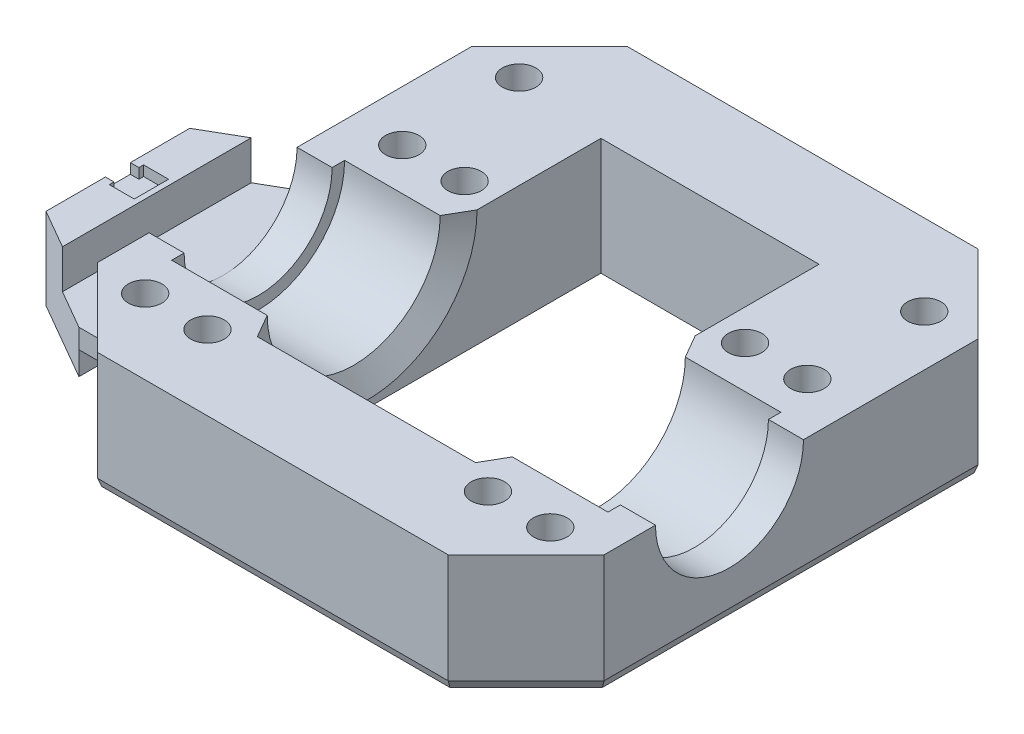
SolidWorks part; units mm, degrees
ref_plane "Спереди" through (0, 0, 0) normal (0, 0, 1) x (1, 0, 0)
ref_plane "Сверху" through (0, 0, 0) normal (0, 1, 0) x (1, 0, 0)
ref_plane "Справа" through (0, 0, 0) normal (1, 0, 0) x (0, 0, -1)
sketch "Sketch1" plane through (0, 0, 0) normal (0, 1, 0) x (1, 0, 0)
  line L1 (32.5, -50) -> (-32.5, -50)
  line L2 (32.5, -50) -> (32.5, 50)
  line L3 (32.5, 50) -> (-32.5, 50)
  line L4 (-32.5, -50) -> (-32.5, 50)
  line L5 (32.5, -50) -> (-32.5, 50) construction
  line L6 (32.5, 50) -> (-32.5, -50) construction
  line L7 (14, -40) -> (-14, -40)
  line L8 (14, -40) -> (14, 40)
  line L9 (14, 40) -> (-14, 40)
  line L10 (-14, -40) -> (-14, 40)
  line L11 (14, -40) -> (-14, 40) construction
  line L12 (14, 40) -> (-14, -40) construction
  point P0 (0, 0)
  point P6 (0, 0)
  dimension "D1" = 65
  dimension "D2" = 100
  dimension "D3" = 80
  dimension "D4" = 28
extrude "Boss-Extrude1" add sketch "Sketch1" along normal blind 15
sketch "Sketch3" plane through (0, 15, 0) normal (0, 1, 0) x (1, 0, 0)
  line L0 (-14, 0) -> (-32.5, 0) construction
  line L1 (-14, 40) -> (-14, -40) construction
  line L2 (-32.5, 50) -> (-32.5, -50) construction
  line L3 (14, 0) -> (32.5, 0) construction
  line L4 (14, -40) -> (14, 40) construction
  line L5 (32.5, -50) -> (32.5, 50) construction
  line L10 (14, -11.1) -> (28, -11.1)
  line L11 (14, -11.1) -> (14, 0)
  line L12 (14, 0) -> (28, 0)
  line L13 (28, -11.1) -> (28, 0)
  line L14 (14, -11.1) -> (28, 0) construction
  line L15 (14, 0) -> (28, -11.1) construction
  line L16 (-28, -11.1) -> (-14, -11.1)
  line L17 (-28, -11.1) -> (-28, 0)
  line L18 (-28, 0) -> (-14, 0)
  line L19 (-14, -11.1) -> (-14, 0)
  line L20 (-28, -11.1) -> (-14, 0) construction
  line L21 (-28, 0) -> (-14, -11.1) construction
  point P18 (21, -5.55)
  point P23 (-21, -5.55)
  dimension "D1" = 14
  dimension "D2" = 11.1
revolve "Cut-Revolve1" cut sketch "Sketch3" angle 360 about L12
sketch "Sketch4" plane through (32.5, 0, 0) normal (1, 0, 0) x (0, 0, -1)
  line L0 (-50, 15) -> (50, 15) construction
  circle A0 centre (0, 15) radius 9.5
  dimension "D1" = 19
extrude "Cut-Extrude2" cut sketch "Sketch4" against normal through all
sketch "Sketch8" plane through (0, 15, 0) normal (0, 1, 0) x (1, 0, 0)
  line L0 (-18, 16.5) -> (-26, 16.5) construction
  line L1 (-18, -16.5) -> (18, -16.5) construction
  line L2 (-18, -16.5) -> (-18, 16.5) construction
  line L3 (-18, 16.5) -> (18, 16.5) construction
  line L4 (18, -16.5) -> (18, 16.5) construction
  line L5 (-18, -16.5) -> (18, 16.5) construction
  line L6 (-18, 16.5) -> (18, -16.5) construction
  line L7 (-9, 27) -> (9, 27) construction
  line L8 (-9, 27) -> (-9, -27) construction
  line L9 (-9, -27) -> (9, -27) construction
  line L10 (9, 27) -> (9, -27) construction
  line L11 (-9, 27) -> (9, -27) construction
  line L12 (-9, -27) -> (9, 27) construction
  line L13 (18, 16.5) -> (26, 16.5) construction
  line L14 (18, -16.5) -> (26, -16.5) construction
  line L15 (-18, -16.5) -> (-26, -16.5) construction
  circle A0 centre (18, 16.5) radius 2.15
  circle A1 centre (18, -16.5) radius 2.15
  circle A2 centre (-18, -16.5) radius 2.15
  circle A3 centre (-18, 16.5) radius 2.15
  circle A4 centre (9, -27) radius 2.15
  circle A5 centre (-9, -27) radius 2.15
  circle A6 centre (-9, 27) radius 2.15
  circle A7 centre (9, 27) radius 2.15
  circle A8 centre (-26, 16.5) radius 2.15
  circle A9 centre (26, 16.5) radius 2.15
  circle A10 centre (26, -16.5) radius 2.15
  circle A11 centre (-26, -16.5) radius 2.15
  point P0 (0, 0)
  point P10 (0, 0)
  dimension "D3" = 4.3
  dimension "D1" = 33
  dimension "D2" = 36
  dimension "D4" = 18
  dimension "D5" = 54
  dimension "D6" = 8
extrude "Cut-Extrude6" cut sketch "Sketch8" against normal through all
fillet "Fillet1" radius 20 4 edges at (-32.5, 7.5, 50) (-32.5, 7.5, -50) (32.5, 7.5, -50) (32.5, 7.5, 50)
chamfer "Chamfer1" distance 3 angle 30 2 edges at (-14, 3.9, 0) (14, 3.9, 0)
sketch "Sketch10" plane through (-32.5, 0, 0) normal (-1, 0, 0) x (0, 0, 1)
  line L0 (-9.5, 15) -> (9.5, 15) construction
  line L1 (0, 15) -> (0, 0) construction
  line L2 (-30, 0) -> (30, 0) construction
  line L4 (15, 5.5) -> (-15, 5.5)
  line L5 (15, 5.5) -> (15, 0)
  line L6 (15, 0) -> (-15, 0)
  line L7 (-15, 5.5) -> (-15, 0)
  line L8 (15, 5.5) -> (-15, 0) construction
  line L9 (15, 0) -> (-15, 5.5) construction
  arc A0 (-9.5, 15) -> (9.5, 15) centre (0, 15) ccw construction
  point P8 (0, 2.75)
  dimension "D1" = 30
extrude "Boss-Extrude2" add sketch "Sketch10" along normal blind 13.5
sketch "Sketch12" plane through (-32.5, 0, 0) normal (-1, 0, 0) x (0, 0, 1)
  line L0 (-9.5, 15) -> (9.5, 15) construction
  line L1 (0, 15) -> (0, 0) construction
  line L3 (15, 9.2) -> (-15, 9.2)
  line L4 (15, 9.2) -> (15, 5.5)
  line L5 (15, 5.5) -> (-15, 5.5)
  line L6 (-15, 9.2) -> (-15, 5.5)
  line L7 (15, 9.2) -> (-15, 5.5) construction
  line L8 (15, 5.5) -> (-15, 9.2) construction
  point P7 (0, 7.35)
  dimension "D1" = 5.8
extrude "Boss-Extrude3" add sketch "Sketch12" along normal up to surface (6.5 mm away) from offset 7 up to face at (-46, 2.75, 0)
sketch "Sketch13" plane through (0, 9.2, 0) normal (0, 1, 0) x (1, 0, 0)
  line L0 (-39.5, 0) -> (-46, 0) construction
  line L1 (-39.5, -15) -> (-39.5, 15) construction
  line L2 (-46, 15) -> (-46, -15) construction
  line L3 (-44.9, 2.2) -> (-44.9, 1.6)
  line L4 (-44.9, -2.2) -> (-41.7, -2.2)
  line L5 (-44.9, 1.6) -> (-46, 1.6)
  line L6 (-44.9, 2.2) -> (-41.7, 2.2)
  line L7 (-41.7, -2.2) -> (-41.7, 2.2)
  line L8 (-44.9, -2.2) -> (-41.7, 2.2) construction
  line L9 (-44.9, 2.2) -> (-41.7, -2.2) construction
  line L10 (-44.9, -2.2) -> (-44.9, -1.6)
  line L11 (-44.9, -1.6) -> (-46, -1.6)
  line L12 (-46, -1.6) -> (-46, -15)
  line L13 (-46, -15) -> (-39, -15)
  line L14 (-39, -15) -> (-39, 15)
  line L15 (-39, 15) -> (-46, 15)
  line L16 (-46, 15) -> (-46, 1.6)
  point P6 (-43.3, 0)
  dimension "D1" = 3.2
  dimension "D2" = 4.4
  dimension "D3" = 3.2
  dimension "D4" = 2.7
  dimension "D5" = 7
extrude "Boss-Extrude4" add sketch "Sketch13" along normal blind 1.3
chamfer "Chamfer3" distance 10 angle 30 4 edges at (-39, 9.85, 15) (-46, 5.25, 15) (-46, 5.25, -15) (-39, 9.85, -15)
sketch "Sketch15" plane through (-14, 0, 0) normal (1, 0, 0) x (0, 0, -1)
  line L0 (-12.8, 9.0865) -> (-12.8, 0)
  line L1 (40, 0) -> (-40, 0) construction
  line L2 (-12.8, 0) -> (-40, 0)
  line L3 (-40, 0) -> (-40, 15)
  line L4 (-40, 15) -> (-14.1, 15)
  arc A0 (-14.1, 15) -> (-12.8, 9.0865) centre (0, 15) ccw
  arc A1 (-14.1, 15) -> (14.1, 15) centre (0, 15) ccw construction
  dimension "D1" = 27.2
extrude "Boss-Extrude6" add sketch "Sketch15" along normal up to surface (28 mm away) up to face at (14, 7.65, 0)
sketch "Sketch16" plane through (0, 15, 0) normal (0, 1, 0) x (1, 0, 0)
  line L0 (-32.5, -26.1) -> (32.5, -26.1)
  line L1 (-32.5, -9.5) -> (-32.5, -30) construction
  line L2 (32.5, -30) -> (32.5, -9.5) construction
  line L3 (32.5, -26.1) -> (32.5, -52.2841)
  line L4 (32.5, -52.2841) -> (-32.5, -52.2841)
  line L5 (-32.5, -52.2841) -> (-32.5, -26.1)
  line L7 (-28, -11.1) -> (-15.7321, -11.1) construction
  dimension "D1" = 15
extrude "Cut-Extrude7" cut sketch "Sketch16" against normal through all
sketch "Sketch17" plane through (0, 15, 0) normal (0, 1, 0) x (1, 0, 0)
  line L0 (-14, 40) -> (14, 40)
  line L1 (14, 40) -> (14, 30)
  line L2 (14, 14.1) -> (14, 40) construction
  line L3 (14, 30) -> (-14, 30)
  line L4 (-14, 40) -> (-14, 14.1) construction
  line L5 (-14, 30) -> (-14, 40)
  dimension "D1" = 10
extrude "Boss-Extrude7" add sketch "Sketch17" against normal up to surface (15 mm away) up to face at (0, 0, -13.6)
sketch "Sketch18" plane through (0, 15, 0) normal (0, 1, 0) x (1, 0, 0)
  line L0 (-32.5, 30) -> (-32.5, 50)
  line L1 (-32.5, 50) -> (32.5, 50)
  line L2 (32.5, 50) -> (32.5, 30)
  line L3 (32.5, 30) -> (-32.5, 30)
  line L4 (12.5, 50) -> (-12.5, 50) construction
extrude "Boss-Extrude8" add sketch "Sketch18" against normal up to surface (15 mm away) up to face at (0, 0, -8.6)
sketch "Sketch19" plane through (0, 15, 0) normal (0, 1, 0) x (1, 0, 0)
  line L0 (-32.5, 50) -> (-32.5, 41.9)
  line L1 (-32.5, 50) -> (-32.5, 9.5) construction
  line L2 (-32.5, 41.9) -> (32.5, 41.9)
  line L3 (32.5, 9.5) -> (32.5, 50) construction
  line L4 (32.5, 41.9) -> (32.5, 50)
  line L5 (32.5, 50) -> (-32.5, 50)
  line L6 (-14, 30) -> (14, 30) construction
  dimension "D1" = 11.9
extrude "Cut-Extrude8" cut sketch "Sketch19" against normal through all
sketch "Sketch21" plane through (0, 0, 0) normal (0, -1, 0) x (1, 0, 0)
  line L0 (-32.5, 15) -> (-32.5, -8.25)
  line L1 (-32.5, 15) -> (-36, 15)
  line L2 (-36, 15) -> (-36, 1.75)
  line L3 (-36, 1.75) -> (-46, 1.75)
  line L4 (-46, -9.2265) -> (-46, 9.2265) construction
  line L5 (-46, 1.75) -> (-46, -1.75)
  line L6 (-32.5, -8.25) -> (-46, -8.25)
  line L7 (-46, -8.25) -> (-46, 1.75)
  point P0 (-46, 0)
  point P13 (-46, 0)
  line M17 (-32.5, 15) -> (-36, 15)
  line M19 (-46, 9.2265) -> (-46, -9.2265)
  dimension "D1" = 10
extrude "Cut-Extrude10" cut sketch "Sketch21" against normal blind 3 contours L6 L0 L2 L3 M17 M19
chamfer "Chamfer5" distance 10 angle 45 4 edges at (-32.5, 7.5, 26.1) (32.5, 7.5, 26.1) (32.5, 7.5, -41.9) (-32.5, 7.5, -41.9)
chamfer "Chamfer6" distance 1 angle 20 8 edges at (-27.5, 0, 21.1) (0, 0, 26.1) (27.5, 0, 21.1) (-32.5, 0, -23.45) (-27.5, 0, -36.9) (32.5, 0, -7.9) (27.5, 0, -36.9) (0, 0, -41.9)
sketch "Sketch26" plane through (0, 15, 0) normal (0, 1, 0) x (1, 0, 0)
  line L0 (0, 41.9) -> (0, -26.1) construction
  line L1 (-22.5, 41.9) -> (22.5, 41.9) construction
  line L2 (22.5, -26.1) -> (-22.5, -26.1) construction
  line L3 (26, 31.5) -> (-26, 31.5) construction
  line L4 (26, 16.5) -> (26, 31.5) construction
  line L5 (28.15, -16.5) -> (23.85, -16.5) construction
  circle A0 centre (-26, 31.5) radius 2.15
  circle A1 centre (26, 31.5) radius 2.15
  circle A2 centre (-26, 16.5) radius 2.15 construction
  circle A3 centre (26, -16.5) radius 2.15 construction
  point P9 (0, 31.5)
  point P20 (26, -16.5)
  dimension "D1" = 48
extrude "Cut-Extrude11" cut sketch "Sketch26" against normal through all
chamfer "Chamfer7" distance 0.6 angle 20 10 edges at (26, 0, 18.65) (18, 0, 18.65) (-26, 0, 18.65) (-18, 0, 18.65) (-18, 0, -14.35) (-26, 0, -14.35) (-26, 0, -29.35) (18, 0, -14.35) (26, 0, -14.35) (26, 0, -29.35)
sketch "Sketch27" plane through (0, 10.5, 0) normal (0, 1, 0) x (1, 0, 0)
  line L0 (-39, 13.2679) -> (-39, -13.2679)
  line L1 (-39, -13.2679) -> (-41, -12.1132)
  line L2 (-46, -9.2265) -> (-39, -13.2679) construction
  line L3 (-41, -12.1132) -> (-41, 12.1132)
  line L4 (-39, 13.2679) -> (-46, 9.2265) construction
  line L5 (-41, 12.1132) -> (-39, 13.2679)
  dimension "D1" = 2
extrude "Cut-Extrude12" cut sketch "Sketch27" against normal up to surface (5 mm away) up to face at (-35.5, 5.5, 0)
